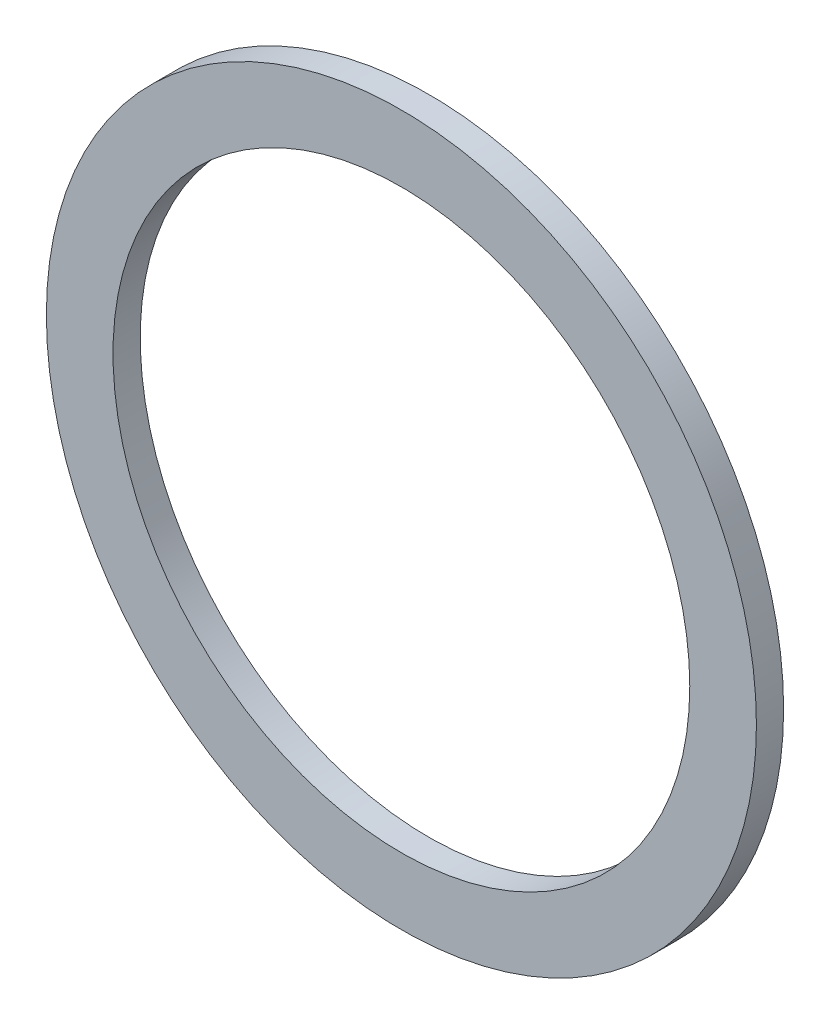
SolidWorks part; units mm, degrees
ref_plane "Přední rovina" through (0, 0, 0) normal (0, 0, 1) x (1, 0, 0)
ref_plane "Horní rovina" through (0, 0, 0) normal (0, 1, 0) x (1, 0, 0)
ref_plane "Pravá rovina" through (0, 0, 0) normal (1, 0, 0) x (0, 0, -1)
sketch "Skica1" plane through (0, 0, 0) normal (0, 0, 1) x (1, 0, 0)
  circle A0 centre (0, 0) radius 10.6
  circle A1 centre (0, 0) radius 13.05
  dimension "D1" = 21.2
  dimension "D2" = 26.1
extrude "Přidat vysunutím1" add sketch "Skica1" along normal blind 1
